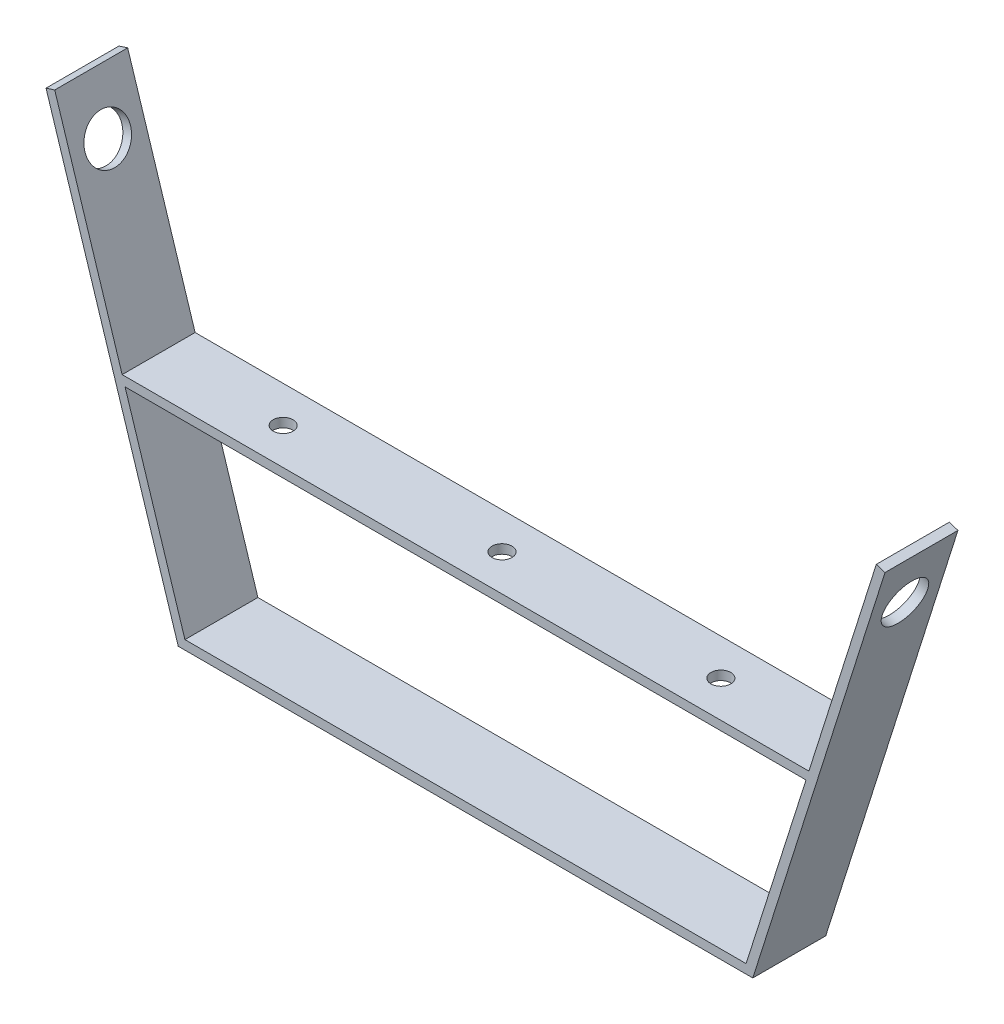
SolidWorks part; units mm, degrees
ref_plane "Front Plane" through (0, 0, 0) normal (0, 0, 1) x (1, 0, 0)
ref_plane "Top Plane" through (0, 0, 0) normal (0, 1, 0) x (1, 0, 0)
ref_plane "Right Plane" through (0, 0, 0) normal (1, 0, 0) x (0, 0, -1)
sketch "Sketch1" plane through (0, 0, 0) normal (0, 0, 1) x (1, 0, 0)
  line L0 (-95.9147, -24.4509) -> (104.1103, -24.4509)
  line L1 (104.1103, -24.4509) -> (150.1478, 120.8292)
  line L2 (-95.9147, -24.4509) -> (-141.9522, 120.8292)
  line L3 (101.7858, -21.2759) -> (147.1211, 121.7883)
  line L4 (-93.5902, -21.2759) -> (101.7858, -21.2759)
  line L5 (-93.5902, -21.2759) -> (-138.9256, 121.7883)
  line L6 (-141.9522, 120.8292) -> (-138.9256, 121.7883)
  line L7 (147.1211, 121.7883) -> (150.1478, 120.8292)
  dimension "D1" = 152.4
  dimension "D2" = 152.4
  dimension "D3" = 200.025
  dimension "D4" = 292.1
  dimension "D5" = 3.175
extrude "Boss-Extrude1" add sketch "Sketch1" along normal blind 25.4
sketch "Sketch2" plane through (-94.2032, -29.8519, 0) normal (-0.9533, -0.3021, 0) x (0, 0, 1)
  line L0 (25.4, 5.6656) -> (0, 5.6656) construction
  line L1 (0, 158.0656) -> (0, 5.6656) construction
  circle A0 centre (12.7, 139.0156) radius 7.9375
  dimension "D3" = 15.875
  dimension "D1" = 133.35
  dimension "D2" = 12.7
extrude "Cut-Extrude1" cut sketch "Sketch2" against normal blind 25.4
sketch "Sketch3" plane through (101.6509, -32.2119, 0) normal (0.9533, -0.3021, 0) x (0, 0, -1)
  line L0 (-25.4, 8.1414) -> (0, 8.1414) construction
  line L1 (-25.4, 8.1414) -> (-25.4, 160.5414) construction
  circle A0 centre (-12.7, 141.4914) radius 7.9375
  dimension "D2" = 15.875
  dimension "D1" = 133.35
  dimension "D3" = 12.7
extrude "Cut-Extrude2" cut sketch "Sketch3" against normal blind 25.4
sketch "Sketch5" plane through (0, 0, 0) normal (0, 0, -1) x (-1, 0, 0)
  line L0 (-123.642, 47.6955) -> (115.4464, 47.6955)
  line L3 (-147.1211, 121.7883) -> (-101.7858, -21.2759) construction
  line L4 (93.5902, -21.2759) -> (138.9256, 121.7883) construction
  line L5 (-122.6359, 44.5205) -> (114.4403, 44.5205)
  line L6 (-123.642, 47.6955) -> (-122.6359, 44.5205)
  line L7 (115.4464, 47.6955) -> (114.4403, 44.5205)
  dimension "D1" = 3.175
  dimension "D2" = 77.724
extrude "Boss-Extrude2" add sketch "Sketch5" against normal blind 25.4
sketch "Sketch6" plane through (0, 47.6955, 0) normal (0, 1, 0) x (1, 0, 0)
  line L0 (-115.4464, -25.4) -> (123.642, -25.4) construction
  line L1 (-84.803, -25.4) -> (92.997, -25.4)
  line L2 (-84.803, -25.4) -> (-84.803, 0)
  line L3 (-84.803, 0) -> (92.997, 0)
  line L4 (92.997, -25.4) -> (92.997, 0)
  line L5 (-115.4464, 0) -> (123.642, 0) construction
  line L6 (123.642, -25.4) -> (123.642, 0) construction
  circle A0 centre (80.297, -12.7) radius 3.4576
  circle A1 centre (4.097, -12.7) radius 3.4576
  circle A2 centre (-72.103, -12.7) radius 3.4576
  point P8 (4.097, -12.7)
  dimension "D1" = 119.545
  dimension "D2" = 88.9
  dimension "D3" = 88.9
  dimension "D4" = 12.7
  dimension "D5" = 12.7
  dimension "D6" = 12.7
extrude "Cut-Extrude4" cut sketch "Sketch6" against normal blind 3.175 contours A2 | A1 | A0
